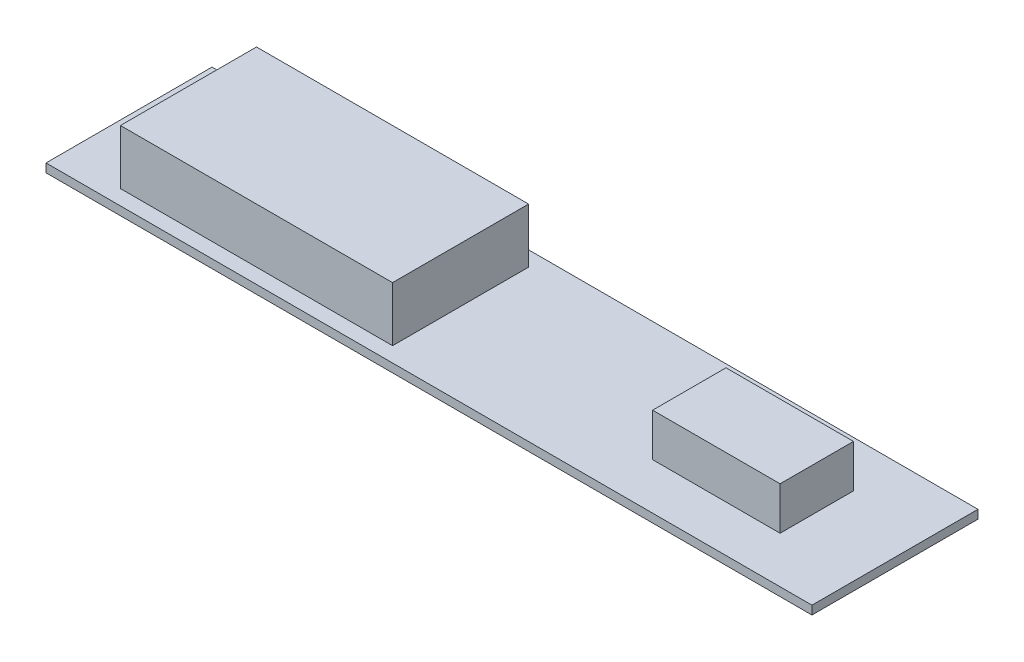
SolidWorks part; units mm, degrees
ref_plane "Front Plane" through (0, 0, 0) normal (0, 0, 1) x (1, 0, 0)
ref_plane "Top Plane" through (0, 0, 0) normal (0, 1, 0) x (1, 0, 0)
ref_plane "Right Plane" through (0, 0, 0) normal (1, 0, 0) x (0, 0, -1)
sketch "Sketch1" plane through (0, 0, 0) normal (0, 1, 0) x (1, 0, 0)
  line L1 (-71.5, -15.5) -> (71.5, -15.5)
  line L2 (-71.5, -15.5) -> (-71.5, 15.5)
  line L3 (-71.5, 15.5) -> (71.5, 15.5)
  line L4 (71.5, -15.5) -> (71.5, 15.5)
  line L5 (-71.5, -15.5) -> (71.5, 15.5) construction
  line L6 (-71.5, 15.5) -> (71.5, -15.5) construction
  point P0 (0, 0)
  dimension "D1" = 143
  dimension "D2" = 31
extrude "Boss-Extrude1" add sketch "Sketch1" along normal blind 1.6
sketch "Sketch2" plane through (0, 1.6, 0) normal (0, 1, 0) x (1, 0, 0)
  line L1 (33.1, -6.85) -> (56.9, -6.85)
  line L2 (33.1, -6.85) -> (33.1, 6.85)
  line L3 (33.1, 6.85) -> (56.9, 6.85)
  line L4 (56.9, -6.85) -> (56.9, 6.85)
  line L5 (33.1, -6.85) -> (56.9, 6.85) construction
  line L6 (33.1, 6.85) -> (56.9, -6.85) construction
  point P0 (45, 0)
  dimension "D1" = 23.8
  dimension "D2" = 13.7
  dimension "D3" = 45
extrude "Boss-Extrude2" add sketch "Sketch2" along normal blind 8
sketch "Sketch3" plane through (0, 1.6, 0) normal (0, 1, 0) x (1, 0, 0)
  line L1 (-60.4, -12.7) -> (-9.6, -12.7)
  line L2 (-60.4, -12.7) -> (-60.4, 12.7)
  line L3 (-60.4, 12.7) -> (-9.6, 12.7)
  line L4 (-9.6, -12.7) -> (-9.6, 12.7)
  line L5 (-60.4, -12.7) -> (-9.6, 12.7) construction
  line L6 (-60.4, 12.7) -> (-9.6, -12.7) construction
  point P0 (-35, 0)
  dimension "D1" = 50.8
  dimension "D2" = 25.4
  dimension "D3" = 35
extrude "Boss-Extrude3" add sketch "Sketch3" along normal blind 10.2
